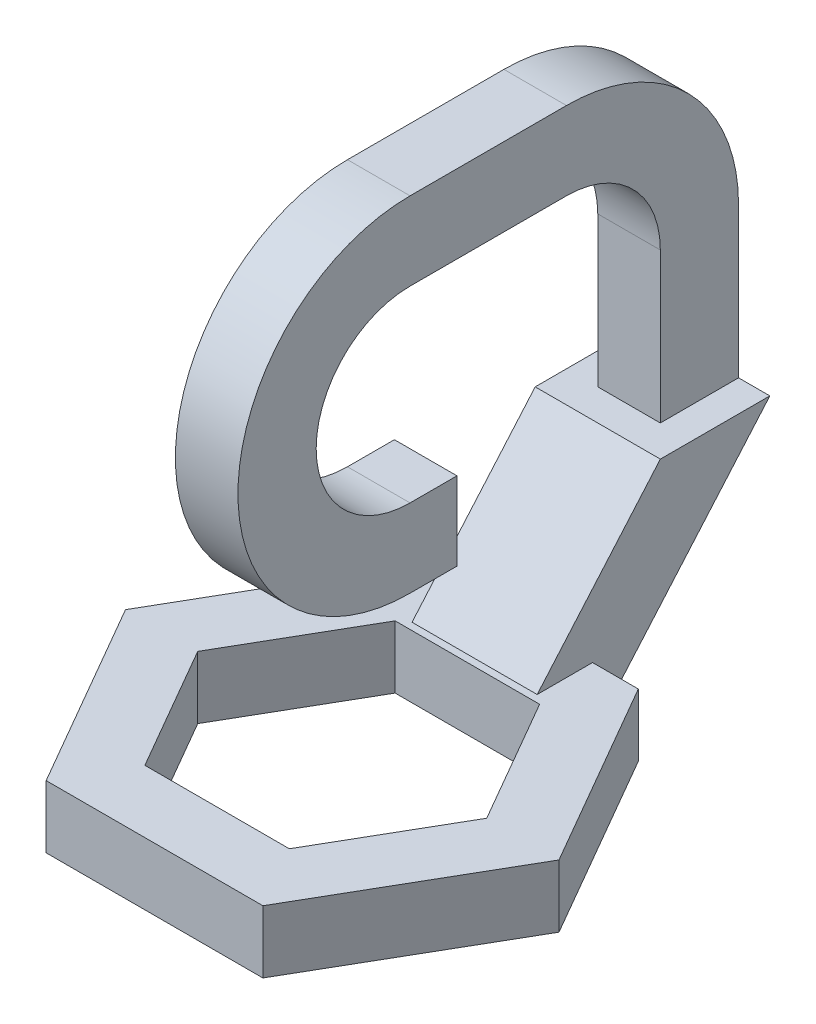
SolidWorks part; units mm, degrees
ref_plane "Alzado" through (0, 0, 0) normal (0, 0, 1) x (1, 0, 0)
ref_plane "Planta" through (0, 0, 0) normal (0, 1, 0) x (1, 0, 0)
ref_plane "Vista lateral" through (0, 0, 0) normal (1, 0, 0) x (0, 0, -1)
sketch "Croquis1" plane through (0, 0, 0) normal (0, 1, 0) x (1, 0, 0)
  line L0 (0, 0) -> (0, 159.9756) construction
  line L1 (-138.55, 239.9756) -> (-277.1, 0)
  line L2 (-277.1, 0) -> (-138.55, -239.9756)
  line L3 (-138.55, -239.9756) -> (138.55, -239.9756)
  line L4 (138.55, -239.9756) -> (277.1, 0)
  line L5 (277.1, 0) -> (138.55, 239.9756)
  line L6 (138.55, 239.9756) -> (-138.55, 239.9756)
  line L7 (-92.362, 159.9756) -> (-184.724, 0)
  line L8 (-184.724, 0) -> (-92.362, -159.9756)
  line L9 (-92.362, -159.9756) -> (92.362, -159.9756)
  line L10 (92.362, -159.9756) -> (184.724, 0)
  line L11 (184.724, 0) -> (92.362, 159.9756)
  line L12 (92.362, 159.9756) -> (-92.362, 159.9756)
  line L13 (0, 159.9756) -> (0, 239.9756) construction
  circle A0 centre (0, 0) radius 239.9756 construction
  circle A1 centre (0, 0) radius 159.9756 construction
  dimension "D1" = 277.1
  dimension "D2" = 80
extrude "Saliente-Extruir1" add sketch "Croquis1" along normal blind 80
sketch "Croquis2" plane through (0, 0, 0) normal (1, 0, 0) x (0, 0, -1)
  line L0 (239.9756, 0) -> (466.6756, 261.9)
  line L1 (466.6756, 261.9) -> (326.6756, 261.9)
  line L2 (326.6756, 261.9) -> (169.2234, 80)
  line L4 (0, 80) -> (239.9756, 80) construction
  line L9 (169.2234, 80) -> (169.2234, 0)
  line L10 (0, 0) -> (239.9756, 0) construction
  line L11 (169.2234, 0) -> (239.9756, 0)
  dimension "D1" = 226.7
  dimension "D2" = 261.9
  dimension "D3" = 140
extrude "Saliente-Extruir2" add sketch "Croquis2" along normal mid plane 160
sketch "Croquis3" plane through (0, 0, 0) normal (1, 0, 0) x (0, 0, -1)
  line L0 (366.6756, 453.4) -> (366.6756, 261.9)
  line L1 (46.6756, 453.4) -> (46.6756, 233.4) construction
  line L2 (466.6756, 261.9) -> (326.6756, 261.9) construction
  line L3 (246.6756, 673.4) -> (46.6756, 673.4)
  line L4 (46.6756, 673.4) -> (46.6756, 453.4) construction
  line L5 (246.6756, 673.4) -> (246.6756, 453.4) construction
  line L6 (246.6756, 453.4) -> (466.6756, 453.4) construction
  line L7 (46.6756, 233.4) -> (106.6756, 233.4)
  line L8 (246.6756, 573.4) -> (46.6756, 573.4)
  line L9 (46.6756, 333.4) -> (106.6756, 333.4)
  line L10 (106.6756, 333.4) -> (106.6756, 233.4)
  line L11 (366.6756, 261.9) -> (466.6756, 261.9)
  line L12 (466.6756, 261.9) -> (466.6756, 453.4)
  line L13 (366.6756, 261.9) -> (366.6756, 453.4) construction
  line L14 (466.6756, 261.9) -> (466.6756, 453.4) construction
  arc A0 (46.6756, 673.4) -> (46.6756, 233.4) centre (46.6756, 453.4) ccw
  arc A1 (246.6756, 673.4) -> (466.6756, 453.4) centre (246.6756, 453.4) cw
  arc A2 (246.6756, 573.4) -> (366.6756, 453.4) centre (246.6756, 453.4) cw
  arc A3 (46.6756, 573.4) -> (46.6756, 333.4) centre (46.6756, 453.4) ccw
  dimension "D1" = 220
  dimension "D2" = 60
  dimension "D3" = 373.4
  dimension "D5" = 200
  dimension "D4" = 100
extrude "Saliente-Extruir4" add sketch "Croquis3" along normal mid plane 80
